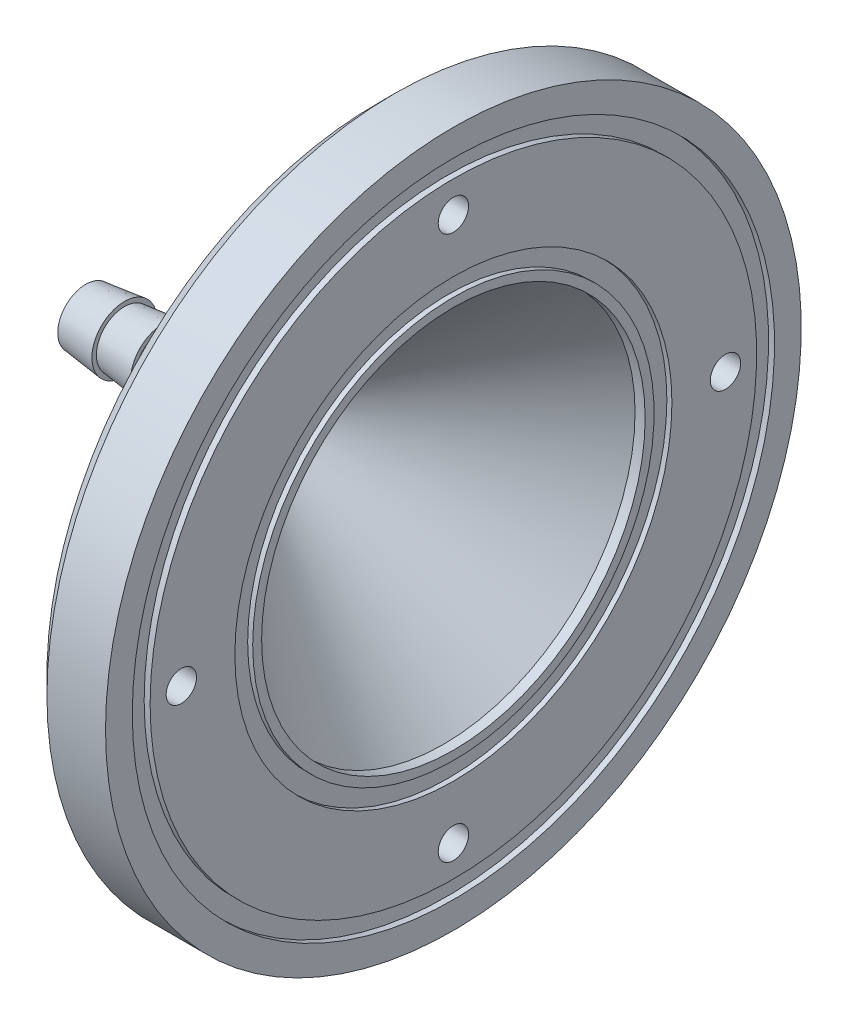
SolidWorks part; units mm, degrees
ref_plane "Front Plane" through (0, 0, 0) normal (0, 0, 1) x (1, 0, 0)
ref_plane "Top Plane" through (0, 0, 0) normal (0, 1, 0) x (1, 0, 0)
ref_plane "Right Plane" through (0, 0, 0) normal (1, 0, 0) x (0, 0, -1)
sketch "Sketch1" plane through (0, 0, 0) normal (0, 0, 1) x (1, 0, 0)
  line L0 (-801.9206, 0) -> (36107.5283, 0) construction
  line L3 (-14.1752, 3.65) -> (-14.1752, 3.15)
  line L8 (-18.5085, 1.9) -> (0, 1.9)
  line L9 (-18.5085, 1.9) -> (-18.5085, 3.15)
  line L10 (22.6971, 24.5) -> (22.6971, 39)
  line L12 (22.6971, 39) -> (14.1311, 39)
  line L16 (22.6971, 24.5) -> (22.1311, 24.5)
  line L17 (22.1311, 24.5) -> (22.1311, 21.5)
  line L18 (14.1311, 39) -> (14.1311, 21.5)
  line L20 (0, 1.9) -> (21.5651, 21.5)
  line L21 (-18.5085, 3.15) -> (-14.1752, 3.65)
  line L22 (21.5651, 21.5) -> (22.1311, 21.5)
  line L23 (-14.1752, 3.15) -> (-9.8419, 3.65)
  line L25 (-9.8419, 3.15) -> (-5.5085, 3.65)
  line L26 (-9.8419, 3.65) -> (-9.8419, 3.15)
  line L27 (-5.5085, 3.65) -> (14.1311, 21.5)
  line L29 (22.0301, 36) -> (22.0301, 34)
  line L30 (22.0301, 34) -> (22.6971, 34)
  line L32 (22.0301, 36) -> (22.6971, 36)
  line L33 (22.1311, 22.5) -> (22.6971, 22.5)
  line L34 (22.6971, 22.5) -> (22.6971, 21.5)
  line L35 (22.6971, 21.5) -> (22.1311, 21.5)
  dimension "D3" = 0.566
  dimension "D2" = 7.3
  dimension "D6" = 3.8
  dimension "D7" = 6.3
  dimension "D5" = 39
  dimension "D8" = 24.5
  dimension "D4" = 5
  dimension "D9" = 0.566
  dimension "D11" = 13
  dimension "D12" = 8.566
  dimension "D14" = 2
  dimension "D13" = 36
  dimension "D15" = 0.667
  dimension "D16" = 1
  dimension "D10" = 2
revolve "Revolve17" add sketch "Sketch1" angle 360 about L0
sketch "Sketch4" plane through (14.1311, 0, 0) normal (-1, 0, 0) x (0, 0, 1)
  line L0 (0, 21.5) -> (0, 39) construction
  circle A0 centre (0, 0) radius 30.5 construction
  circle A1 centre (0, 0) radius 21.5 construction
  circle A2 centre (0, 0) radius 39 construction
  point P3 (0, 30.5)
  point P7 (30.5, 0)
  point P12 (-30.5, 0)
  point P13 (0, -30.5)
  dimension "D1" = 8.5
  dimension "D2" = 8.5
hole_wizard "CBORE for M3 Hex Socket Head Cap Screw2" positions "Sketch4" profile "Sketch5" counterbore size "M3" standard "ISO"
sketch "Sketch5" plane through (14.1311, -30.5, 0) normal (0, 1, 0) x (0, 0, 1)
  line L0 (0, 0) -> (0, 9.5875)
  line L1 (0, 9.5875) -> (1.7, 8.566)
  line L2 (1.7, 8.566) -> (1.7, 3.4)
  line L3 (1.7, 3.4) -> (3.25, 3.4)
  line L4 (3.25, 3.4) -> (3.25, 0)
  line L5 (3.25, 0) -> (0, 0)
  line L10 (0, 9.5875) -> (-1.7, 8.566) construction
  line L11 (0, -6.35) -> (0, 107.95) construction
  dimension "Hole Dia." = 3.4
  dimension "Hole Depth" = 8.566
  dimension "C'Bore Dia." = 6.5
  dimension "C'Bore Depth" = 3.4
  dimension "Drill Angle" = 118
chamfer "Chamfer1" distance 2 angle 45 1 edges at (14.1311, 0, 39)
sketch "Sketch6" plane through (22.6971, 0, 0) normal (1, 0, 0) x (0, 0, -1)
  line L0 (0, 39) -> (0, 24.5)
  circle A0 centre (0, 0) radius 39
  circle A1 centre (0, 0) radius 39 construction
  circle A2 centre (0, 0) radius 24.5 construction
equation "\"D9@Sketch1\"=\"D3@Sketch1\""
